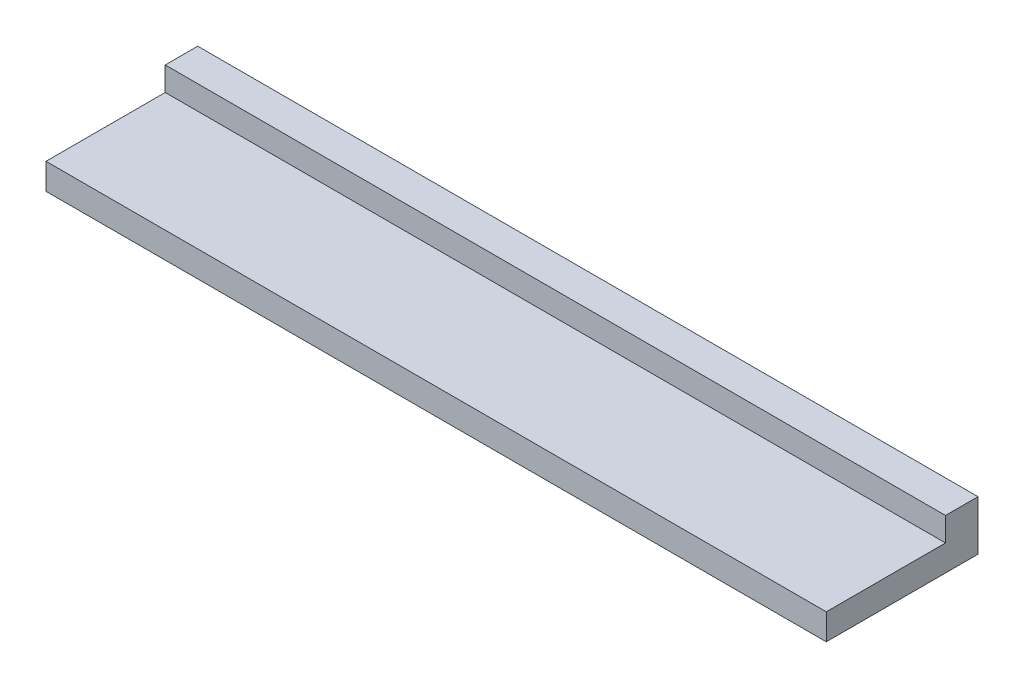
SolidWorks part; units mm, degrees
ref_plane "Спереди" through (0, 0, 0) normal (0, 0, 1) x (1, 0, 0)
ref_plane "Сверху" through (0, 0, 0) normal (0, 1, 0) x (1, 0, 0)
ref_plane "Справа" through (0, 0, 0) normal (1, 0, 0) x (0, 0, -1)
sketch "Эскиз1" plane through (0, 0, 0) normal (0, 1, 0) x (1, 0, 0)
  line L1 (-90, 17.5) -> (90, 17.5)
  line L2 (-90, 17.5) -> (-90, -17.5)
  line L3 (-90, -17.5) -> (90, -17.5)
  line L4 (90, 17.5) -> (90, -17.5)
  line L5 (-90, 17.5) -> (90, -17.5) construction
  line L6 (-90, -17.5) -> (90, 17.5) construction
  point P0 (0, 0)
  dimension "D1" = 180
  dimension "D2" = 35
extrude "Бобышка-Вытянуть1" add sketch "Эскиз1" along normal blind 6
sketch "Эскиз2" plane through (0, 6, 0) normal (0, 1, 0) x (1, 0, 0)
  line L0 (-90, 17.5) -> (-90, 10)
  line L1 (-90, 17.5) -> (-90, -17.5) construction
  line L2 (-90, 10) -> (90, 10)
  line L3 (90, -17.5) -> (90, 17.5) construction
  line L4 (90, 10) -> (90, 17.5)
  line L5 (90, 17.5) -> (-90, 17.5)
  dimension "D1" = 7.5
extrude "Бобышка-Вытянуть2" add sketch "Эскиз2" along normal blind 5.5
